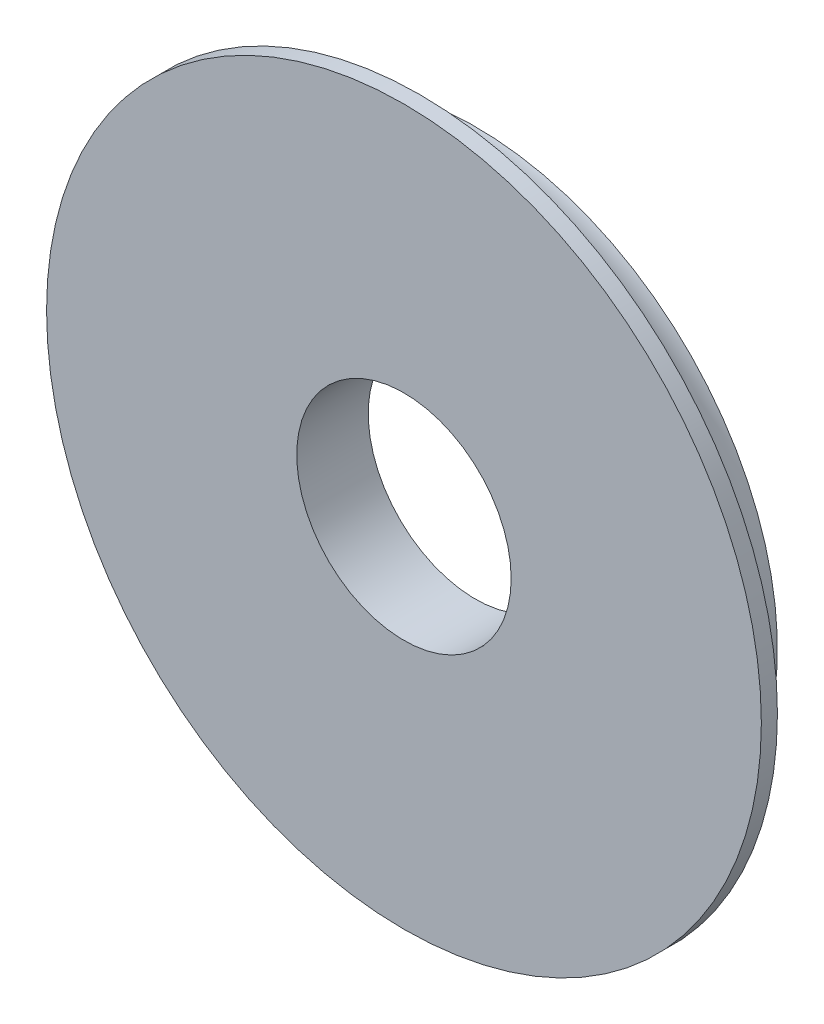
SolidWorks part; units mm, degrees
ref_plane "Front Plane" through (0, 0, 0) normal (0, 0, 1) x (1, 0, 0)
ref_plane "Top Plane" through (0, 0, 0) normal (0, 1, 0) x (1, 0, 0)
ref_plane "Right Plane" through (0, 0, 0) normal (1, 0, 0) x (0, 0, -1)
sketch "Sketch1" plane through (0, 0, 0) normal (0, 0, 1) x (1, 0, 0)
  circle A0 centre (0, 0) radius 10 construction
  circle A1 centre (0, 0) radius 10
  circle A2 centre (0, 0) radius 3
  dimension "D1" = 6
extrude "Boss-Extrude1" add sketch "Sketch1" along normal blind 2
sketch "Sketch2" plane through (0, 0, 0) normal (0, 1, 0) x (1, 0, 0)
  circle A0 centre (10, 0) radius 1.55
  dimension "D1" = 3.1
revolve "Cut-Revolve1" cut sketch "Sketch2" angle 360 about axis through (0, 0, 2) along (0, 0, -1)
